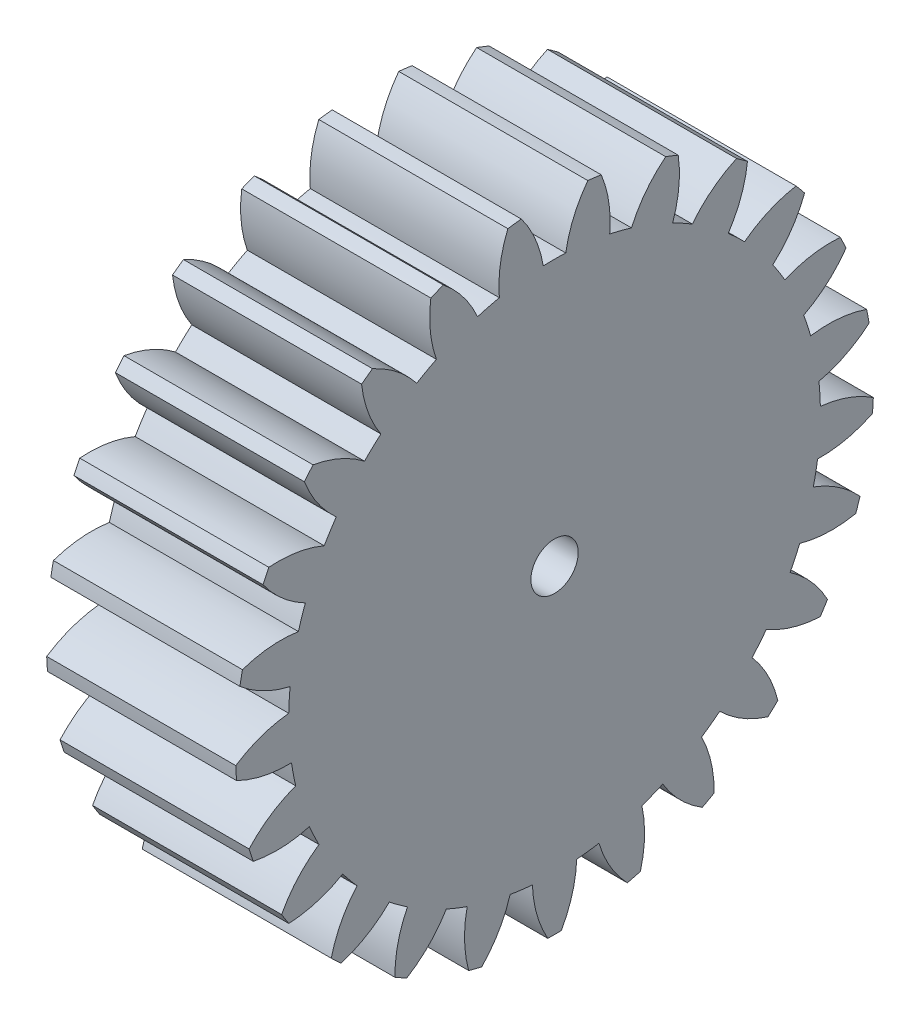
SolidWorks part; units mm, degrees
ref_plane "Plane1" through (0, 0, 0) normal (0, 0, 1) x (1, 0, 0)
ref_plane "Plane2" through (0, 0, 0) normal (0, 1, 0) x (1, 0, 0)
ref_plane "Plane3" through (0, 0, 0) normal (1, 0, 0) x (0, 0, -1)
sketch "HoldingSke" plane through (0, 0, 0) normal (0, 1, 0) x (1, 0, 0)
  line L0 (0, 0) -> (0.3625, -0.169)
  line L1 (-15, 0) -> (100, 0) construction
  line L2 (0, 0) -> (-2.1039, 2.3779)
  line L3 (0, 0) -> (-11.863, 4.5341)
  line L4 (0, 0) -> (7.8269, 3.6497)
  line L5 (0, 0) -> (-46.8476, -17.4728)
  line L6 (0, 0) -> (-16.5793, -11.1861)
  line L7 (-2.1039, 2.3779) -> (8.6586, 51.2059)
  line L8 (-76.2, 54.61) -> (-75.3, 54.61)
  line L9 (-71.009, 38.7566) -> (-53.1078, 45.2721)
  line L10 (-76.2, 71.12) -> (104.1128, 71.12)
  line L11 (0, 0) -> (-20, 0)
  line L12 (-76.2, 101.6) -> (-76.113, 101.6)
  line L13 (24.9733, 27.94) -> (52.9518, 28.4284)
  line L14 (24.9733, 27.94) -> (24.9743, 27.94)
  line L15 (24.9733, 27.94) -> (100.4006, 29.5858)
  line L16 (-63.627, -2.5) -> (-12.827, -2.5)
  circle A0 centre (0, 0) radius 2.5
  circle A1 centre (0, 0) radius 28.124
  circle A2 centre (0, 0) radius 37.5
  circle A3 centre (0, 0) radius 2.5
  dimension "MHD" = 56.248
  dimension "Hub_dia" = 75
  dimension "Bore" = 5
  dimension "MBD" = 5
  dimension "Num_teeth" = 25
  dimension "Pitch" = 0.4
  dimension "Overall_len" = 50
  dimension "Show_teeth" = 25
  dimension "Thickness" = 20
  dimension "OAL" = 50.0001
  dimension "T_dim" = 0.9
  dimension "Ap" = 20
  dimension "H" = 19.05
  dimension "Pitch_radius" = 180.3128
  dimension "Width" = 20
  dimension "Backlash" = 0.087
  dimension "Addendum_fac" = 1
  dimension "Dedendum_fac" = 1.25
  dimension "Clearance_fac" = 0.25
  dimension "Dedendum_add" = 0.001
  dimension "Module" = 2.5
sketch "BasProSke" plane through (0, 0, 0) normal (0, 1, 0) x (1, 0, 0)
  line L0 (-10, 0) -> (60, 0) construction
  line L1 (0, 0) -> (0, 33.75)
  line L2 (0, 0) -> (20, 0)
  line L3 (20, 0) -> (20, 33.75)
  line L4 (20, 33.75) -> (0, 33.75)
  dimension "Thickness" = 20
  dimension "Diameter" = 67.5
revolve "Base-Revolve" add sketch "BasProSke" angle 360 about L0
sketch "TooCutSke" plane through (0, 0, 0) normal (1, 0, 0) x (0, 0, -1)
  line L1 (0, 0) -> (0, 107) construction
  line L2 (0, 0) -> (-2.1144, 31.1784) construction
  line L3 (0, 0) -> (-7.8202, 61.9031) construction
  line L4 (-2.1144, 31.1784) -> (-3.9101, 30.9515) construction
  arc A0 (1.1879, 28.0989) -> (-1.1879, 28.0989) centre (0, 0) ccw
  arc A1 (3.5385, 33.5895) -> (-3.5385, 33.5895) centre (0, 0) ccw
  circle A2 centre (0, 0) radius 31.25 construction
  circle A3 centre (0, 0) radius 29.3654 construction
  arc A4 (-1.1879, 28.0989) -> (-3.5385, 33.5895) centre (-13.5216, 26.0671) ccw
  arc A5 (3.5385, 33.5895) -> (1.1879, 28.0989) centre (13.5216, 26.0671) ccw
  dimension "Root_dia" = 56.248
  dimension "Overcut_dia" = 67.5508
  dimension "Pitch_dia" = 62.5
  dimension "Base_dia" = 58.7308
  dimension "Flank_rad" = 12.5
  dimension "Half_ang" = 7.2
  dimension "Half_CT" = 1.81
extrude "ToothCut" cut sketch "TooCutSke" along normal through all
fillet "Breaks" [suppressed] radius 0.05
fillet "RootFillets" [suppressed] radius 0.626
pattern_circular "TeethCuts" count 25 every 14.4 about axis through (-10, 0, 0) along (1, 0, 0) of "ToothCut", "RootFillets", "Breaks"
sketch "HubNeaOneSke" plane through (0, 0, 0) normal (-1, 0, 0) x (0, 0, 1)
  circle A0 centre (0, 0) radius 28.124
  dimension "Diameter" = 56.248
extrude "HubNearOne" [suppressed] add sketch "HubNeaOneSke" along normal blind 30.0001
sketch "HubNeaBotSke" plane through (0, 0, 0) normal (-1, 0, 0) x (0, 0, 1)
  circle A0 centre (0, 0) radius 28.124
  dimension "Diameter" = 56.248
extrude "HubNearBoth" [suppressed] add sketch "HubNeaBotSke" along normal blind 15
ref_plane "FarPln" through (20, 0, 0) normal (1, 0, 0) x (0, 0, -1)
sketch "HubFarSke" plane through (20, 0, 0) normal (1, 0, 0) x (0, 0, -1)
  circle A0 centre (0, 0) radius 28.124
  dimension "Diameter" = 56.248
extrude "HubFar" [suppressed] add sketch "HubFarSke" along normal blind 15
sketch "BorSke" plane through (0, 0, 0) normal (1, 0, 0) x (0, 0, -1)
  circle A0 centre (0, 0) radius 2.5
  dimension "Diameter" = 5
extrude "Bore" cut sketch "BorSke" along normal mid plane 100.0001
sketch "KeySke" plane through (0, 0, 0) normal (1, 0, 0) x (0, 0, -1)
  line L0 (-1, 0) -> (-1, 3.4)
  line L1 (-1, 3.4) -> (1, 3.4)
  line L2 (1, 3.4) -> (1, 0)
  line L3 (0, 0) -> (0, 34) construction
  line L4 (-1, 0) -> (1, 0)
  dimension "Offset" = 3.4
extrude "Keyway" [suppressed] cut sketch "KeySke" along normal mid plane 100.0001
pattern_circular "Keyway2" [suppressed] count 2 every 90 about axis through (-10, 0, 0) along (1, 0, 0)
equation "' \"Module@HoldingSke\" = 6.35"
equation "' \"Num_teeth@HoldingSke\" = 12"
equation "' \"Ap@HoldingSke\" =  20"
equation "' \"Ap@HoldingSke\" = 20"
equation "' \"Width@HoldingSke\" = 0.5 * 25.4"
equation "' \"Hub_dia@HoldingSke\"= 1 * 25.4"
equation "' \"Hub_dia@HoldingSke\" = 1 * 25.4"
equation "' \"Overall_len@HoldingSke\" = 1.0 * 25.4"
equation "' \"Bore@HoldingSke\" = 0.75 * 25.4"
equation "' \"T_dim@HoldingSke\" = 0.1 * 25.4"
equation "' \"Width@KeySke\" = 0.25 * 25.4"
equation "' \"Show_teeth@HoldingSke\" = 13"
equation "' \"Backlash@HoldingSke\" = 0.009 * 25.4"
equation "' \"Addendum_fac@HoldingSke\" = 1.0"
equation "' \"Dedendum_fac@HoldingSke\" = 1.25"
equation "' \"Dedendum_add@HoldingSke\" = 0.00005 * 25.4"
equation "' \"Clearance_fac@HoldingSke\" = 0.25"
equation "\"Pitch@HoldingSke\" = 1 / \"Module@HoldingSke\""
equation "\"Overcut_dia@TooCutSke\" = (\"Num_teeth@HoldingSke\" + 2 * \"Addendum_fac@HoldingSke\") / \"Pitch@HoldingSke\" + 0.002 * 25.4"
equation "\"Pitch_dia@TooCutSke\" = \"Num_teeth@HoldingSke\" / \"Pitch@HoldingSke\""
equation "\"Base_dia@TooCutSke\" = \"Num_teeth@HoldingSke\" / \"Pitch@HoldingSke\" * cos((\"Ap@HoldingSke\"  * 3.14159265 / 180))"
equation "\"Root_dia@TooCutSke\" = (\"Num_teeth@HoldingSke\" + 2) / \"Pitch@HoldingSke\" - 2 * (\"Addendum_fac@HoldingSke\" + \"Dedendum_fac@HoldingSke\") / \"Pitch@HoldingSke\" - \"Dedendum_add@HoldingSke\" * 2"
equation "\"Half_ang@TooCutSke\" = 180 / \"Num_teeth@HoldingSke\""
equation "\"Half_CT@TooCutSke\" = \"Num_teeth@HoldingSke\" / \"Pitch@HoldingSke\" * sin((3.14159265 / 2 / \"Num_teeth@HoldingSke\")) / 2 - 7 * \"Backlash@HoldingSke\" / 4"
equation "\"Flank_rad@TooCutSke\" = \"Num_teeth@HoldingSke\" / \"Pitch@HoldingSke\" / 5"
equation "\"Radius@RootFillets\" = \"Clearance_fac@HoldingSke\" / \"Pitch@HoldingSke\" + \"Dedendum_add@HoldingSke\""
equation "\"Break_rad@Breaks\" = 0.02 / \"Pitch@HoldingSke\""
equation "\"Thickness@HoldingSke\" = \"Width@HoldingSke\""
equation "\"OAL@HoldingSke\" = \"Thickness@HoldingSke\""
equation "\"MHD@HoldingSke\" = (\"Num_teeth@HoldingSke\" + 2) / \"Pitch@HoldingSke\" - 2 * (\"Addendum_fac@HoldingSke\" + \"Dedendum_fac@HoldingSke\")  / \"Pitch@HoldingSke\" - \"Dedendum_add@HoldingSke\" * 2"
equation "\"MBD@HoldingSke\" = (\"Num_teeth@HoldingSke\" + 2) / \"Pitch@HoldingSke\" - 2 * (\"Addendum_fac@HoldingSke\" + \"Dedendum_fac@HoldingSke\")  / \"Pitch@HoldingSke\" - \"Dedendum_add@HoldingSke\" * 2 - 0.002 * 25.4"
equation "\"MHD@HoldingSke\" = ((sgn( \"MHD@HoldingSke\" - \"Hub_dia@HoldingSke\" )-1)*( \"MHD@HoldingSke\" - \"Hub_dia@HoldingSke\" ))/-2+ \"Hub_dia@HoldingSke\""
equation "\"MBD@HoldingSke\" = ((sgn( \"MBD@HoldingSke\" - \"Bore@HoldingSke\" )-1)*( \"MBD@HoldingSke\" - \"Bore@HoldingSke\" ))/-2+ \"Bore@HoldingSke\""
equation "\"OAL@HoldingSke\" = ((sgn( \"OAL@HoldingSke\" - \"Overall_len@HoldingSke\" )+1)*( \"OAL@HoldingSke\" - \"Overall_len@HoldingSke\" ))/2 + \"Overall_len@HoldingSke\" + 0.000002 * 25.4"
equation "\"Num_teeth@TeethCuts\" = int( \"Show_teeth@HoldingSke\" ) + 1"
equation "\"Num_teeth@TeethCuts\" = ((sgn( \"Num_teeth@TeethCuts\" - \"Num_teeth@HoldingSke\" )-1)*( \"Num_teeth@TeethCuts\" - \"Num_teeth@HoldingSke\" ))/-2+ \"Num_teeth@HoldingSke\""
equation "\"Num_teeth@TeethCuts\" = ((sgn( \"Num_teeth@TeethCuts\" - 2.0)+1)*( \"Num_teeth@TeethCuts\" - 2.0))/2 +2.0"
equation "\"Angle@TeethCuts\" = 360.0 / \"Num_teeth@HoldingSke\""
equation "\"Diameter@BasProSke\" = (\"Num_teeth@HoldingSke\" + 2 * \"Addendum_fac@HoldingSke\") / \"Pitch@HoldingSke\""
equation "\"Thickness@BasProSke\"  = \"Thickness@HoldingSke\""
equation "' \"Fillet_rad@BasProSke\" =  \"Thickness@HoldingSke\" * 0.05"
equation "' \"Fillet_rad@BasProSke\" = \"Thickness@HoldingSke\" * 0.05"
equation "\"MHD@HoldingSke\" = ((sgn( \"MHD@HoldingSke\" - \"Root_dia@TooCutSke\" )-1)*( \"MHD@HoldingSke\" - \"Root_dia@TooCutSke\" ))/-2+ \"Root_dia@TooCutSke\""
equation "\"Diameter@HubNeaOneSke\" = \"MHD@HoldingSke\""
equation "\"Length@HubNearOne\" = \"OAL@HoldingSke\" - \"Thickness@BasProSke\""
equation "\"Diameter@HubNeaBotSke\" = \"MHD@HoldingSke\""
equation "\"Length@HubNearBoth\" = ( \"OAL@HoldingSke\" - \"Thickness@BasProSke\" ) / 2.0"
equation "\"Thickness@FarPln\" = \"Thickness@BasProSke\""
equation "\"Diameter@HubFarSke\" = \"MHD@HoldingSke\""
equation "\"Length@HubFar\" = ( \"OAL@HoldingSke\" - \"Thickness@BasProSke\" ) / 2.0"
equation "\"Diameter@BorSke\" = \"MBD@HoldingSke\""
equation "\"D1@Bore\" = \"OAL@HoldingSke\" * 2.0"
equation "\"D1@Keyway\" = \"OAL@HoldingSke\" * 2.0"
equation "\"Offset@KeySke\" = \"T_dim@HoldingSke\" + \"MBD@HoldingSke\" / 2.0"
